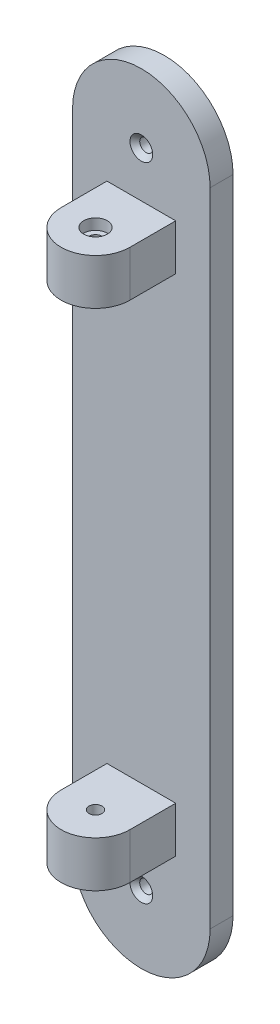
SolidWorks part; units mm, degrees
material "Plain Carbon Steel"
ref_plane "Front Plane" through (0, 0, 0) normal (0, 0, 1) x (1, 0, 0)
ref_plane "Top Plane" through (0, 0, 0) normal (0, 1, 0) x (1, 0, 0)
ref_plane "Right Plane" through (0, 0, 0) normal (1, 0, 0) x (0, 0, -1)
sketch "Sketch1" plane through (0, 0, 0) normal (0, 0, 1) x (1, 0, 0)
  line L1 (0, 0) -> (38.1, 0)
  line L2 (0, 0) -> (0, 88.9)
  line L4 (38.1, 0) -> (38.1, 88.9)
  arc A0 (0, 88.9) -> (38.1, 88.9) centre (19.05, 88.9) cw
  point P6 (0, 0)
  point P7 (0, 0)
  dimension "D3" = 19.05
  dimension "D1" = 38.1
  dimension "D2" = 88.9
extrude "Boss-Extrude1" add sketch "Sketch1" along normal blind 6.35
hole_wizard "CSK for M3 Flat Head Machine Screw1" positions "3DSketch1" profile "Sketch2" countersink size "M3" standard "ANSI Metric" end condition through all
sketch3d "3DSketch1"
  line L0 (19.05, 88.9, 6.35) -> (19.05, 88.9, 0) construction
  point P0 (19.05, 88.9, 6.35)
sketch "Sketch2" plane through (19.05, 88.9, 6.35) normal (1, 0, 0) x (0, -1, 0)
  line L0 (0, 0) -> (0, 6.35)
  line L1 (0, 6.35) -> (1.8, 6.35)
  line L2 (1.8, 6.35) -> (1.8, 1.35)
  line L3 (1.8, 1.35) -> (3.15, 0)
  line L5 (3.15, 0) -> (0, 0)
  line L6 (-1.8, 1.35) -> (-3.15, 0) construction
  line L11 (0, -6.35) -> (0, 107.95) construction
  dimension "Thru Hole Dia." = 3.6
  dimension "Thru Hole Depth" = 6.35
  dimension "Near C'Sink Dia." = 6.3
  dimension "Near C'Sink Angle" = 90
sketch "Sketch3" plane through (0, 0, 6.35) normal (0, 0, 1) x (1, 0, 0)
  line L0 (19.05, 0) -> (19.05, 107.95) construction
  line L5 (0, 0) -> (38.1, 0) construction
  line L7 (28.575, 76.2) -> (9.525, 76.2)
  line L8 (28.575, 76.2) -> (28.575, 63.5)
  line L9 (28.575, 63.5) -> (9.525, 63.5)
  line L10 (9.525, 76.2) -> (9.525, 63.5)
  line L11 (28.575, 76.2) -> (9.525, 63.5) construction
  line L12 (28.575, 63.5) -> (9.525, 76.2) construction
  arc A0 (38.1, 88.9) -> (0, 88.9) centre (19.05, 88.9) ccw construction
  point P0 (19.05, 69.85)
  point P12 (19.05, 63.5)
  dimension "D1" = 63.5
  dimension "D2" = 19.05
  dimension "D3" = 12.7
extrude "Boss-Extrude2" add sketch "Sketch3" along normal blind 12.7
sketch "Sketch6" plane through (0, 76.2, 0) normal (0, 1, 0) x (1, 0, 0)
  line L0 (9.525, -19.05) -> (28.575, -19.05)
  arc A0 (9.525, -19.05) -> (28.575, -19.05) centre (19.05, -19.05) ccw
extrude "Boss-Extrude5" add sketch "Sketch6" against normal up to surface (12.7 mm away) up to face at (19.05, 63.5, 12.7)
hole_wizard "CBORE for M3 SHCS1" positions "Sketch9" profile "Sketch10" counterbore size "M3" standard "ANSI Metric"
sketch "Sketch9" plane through (0, 76.2, 0) normal (0, 1, 0) x (1, 0, 0)
  point P0 (19.05, -19.05)
  point P4 (19.05, -19.05)
sketch "Sketch10" plane through (19.05, 76.2, 19.05) normal (1, 0, 0) x (0, 0, 1)
  line L0 (0, 0) -> (0, 13.7805)
  line L1 (0, 13.7805) -> (1.8, 12.699)
  line L2 (1.8, 12.699) -> (1.8, 3)
  line L3 (1.8, 3) -> (3.25, 3)
  line L4 (3.25, 3) -> (3.25, 0)
  line L5 (3.25, 0) -> (0, 0)
  line L10 (0, 13.7805) -> (-1.8, 12.699) construction
  line L11 (0, -6.35) -> (0, 107.95) construction
  dimension "Hole Dia." = 3.6
  dimension "Hole Depth" = 12.699
  dimension "C'Bore Dia." = 6.5
  dimension "C'Bore Depth" = 3
  dimension "Drill Angle" = 118
mirror "Mirror1" about plane through (0, 0, 0) normal (0, 1, 0) of "Boss-Extrude1", "CSK for M3 Flat Head Machine Screw1", "Boss-Extrude2", "Boss-Extrude5", "CBORE for M3 SHCS1"
